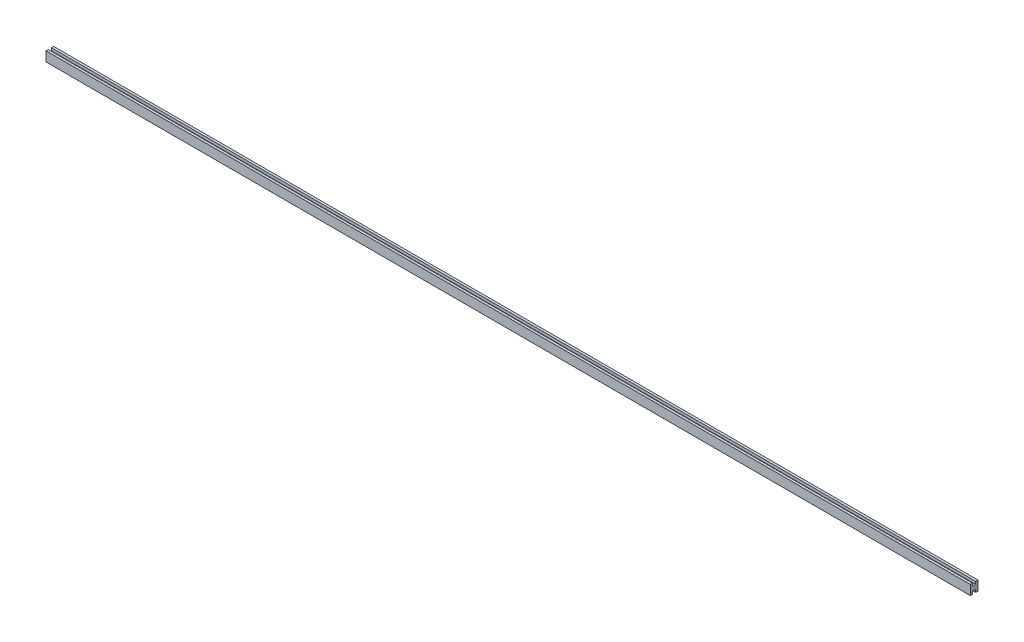
SolidWorks part; units mm, degrees
ref_plane "Front Plane" through (0, 0, 0) normal (0, 0, 1) x (1, 0, 0)
ref_plane "Top Plane" through (0, 0, 0) normal (0, 1, 0) x (1, 0, 0)
ref_plane "Right Plane" through (0, 0, 0) normal (1, 0, 0) x (0, 0, -1)
sketch "Sketch1" plane through (0, 0, 0) normal (1, 0, 0) x (0, 0, -1)
  line L0 (5.08, -15.875) -> (12.7, -15.875)
  line L1 (-12.7, -15.875) -> (-5.08, -15.875)
  line L2 (-12.7, -15.875) -> (-12.7, 15.875)
  line L3 (-12.7, 15.875) -> (-5.08, 15.875)
  line L4 (12.7, -15.875) -> (12.7, 15.875)
  line L5 (-12.7, -15.875) -> (12.7, 15.875) construction
  line L6 (-12.7, 15.875) -> (12.7, -15.875) construction
  line L7 (-5.08, 15.875) -> (-5.08, 6.985)
  line L8 (-5.08, 6.985) -> (5.08, 6.985)
  line L9 (5.08, 6.985) -> (5.08, 15.875)
  line L10 (-12.7, 0) -> (12.7, 0) construction
  line L11 (-5.08, -15.875) -> (-5.08, -6.985)
  line L12 (-5.08, -6.985) -> (5.08, -6.985)
  line L13 (5.08, -6.985) -> (5.08, -15.875)
  line L14 (5.08, 15.875) -> (12.7, 15.875)
  point P0 (0, 0)
  point P17 (0, 0)
extrude "Boss-Extrude1" add sketch "Sketch1" along normal blind 3048 contours L7 L8 L9 L14 L4 L0 L13 L12 L11 L1 L2 L3
